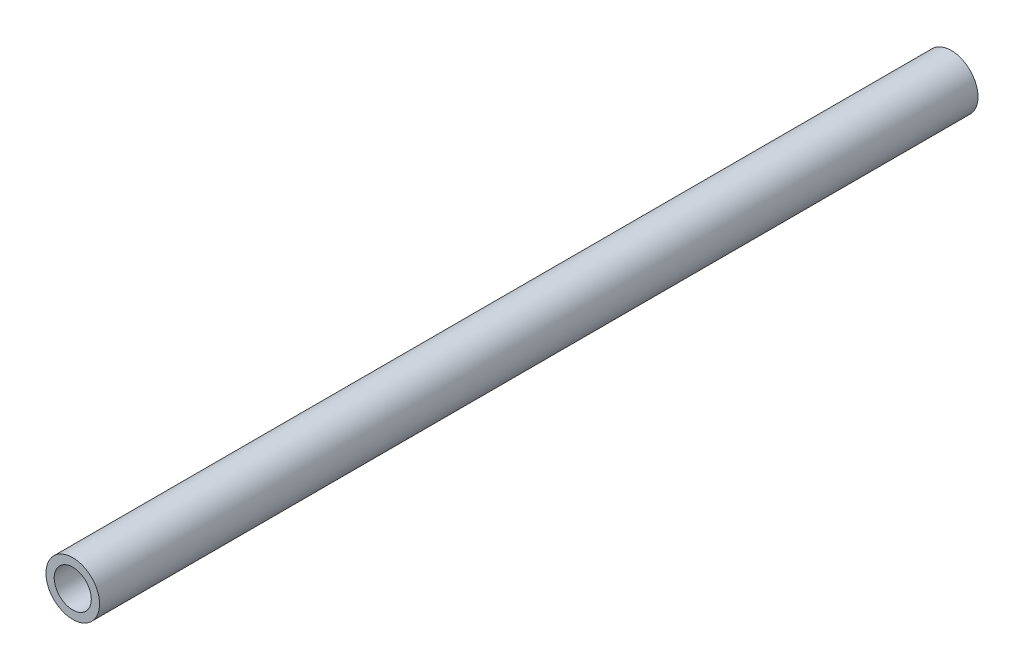
SolidWorks part; units mm, degrees
material "PVC Rigid"
ref_plane "Front Plane" through (0, 0, 0) normal (0, 0, 1) x (1, 0, 0)
ref_plane "Top Plane" through (0, 0, 0) normal (0, 1, 0) x (1, 0, 0)
ref_plane "Right Plane" through (0, 0, 0) normal (1, 0, 0) x (0, 0, -1)
sketch "Sketch1" plane through (0, 0, 0) normal (0, 0, 1) x (1, 0, 0)
  circle A0 centre (0, 0) radius 7.747
  circle A1 centre (0, 0) radius 5.3594
  dimension "D1" = 15.494
  dimension "D2" = 10.7188
extrude "Boss-Extrude1" add sketch "Sketch1" along normal blind 254
